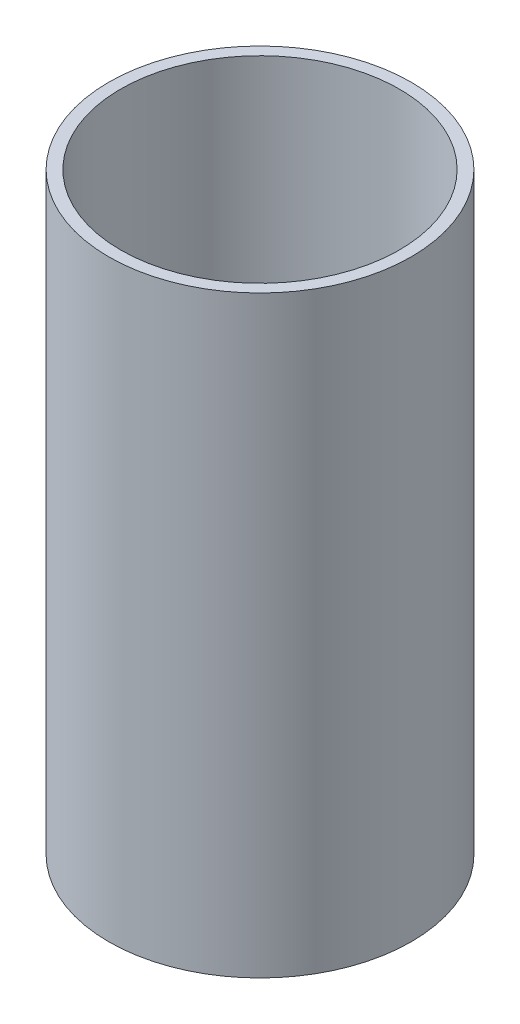
SolidWorks part; units mm, degrees
ref_plane "Front Plane" through (0, 0, 0) normal (0, 0, 1) x (1, 0, 0)
ref_plane "Top Plane" through (0, 0, 0) normal (0, 1, 0) x (1, 0, 0)
ref_plane "Right Plane" through (0, 0, 0) normal (1, 0, 0) x (0, 0, -1)
sketch "Sketch1" plane through (0, 0, 0) normal (0, 1, 0) x (1, 0, 0)
  circle A0 centre (0, 0) radius 23.5
  circle A1 centre (0, 0) radius 25.5
  dimension "D1" = 2
  dimension "D2" = 51
extrude "Boss-Extrude1" add sketch "Sketch1" along normal blind 100
